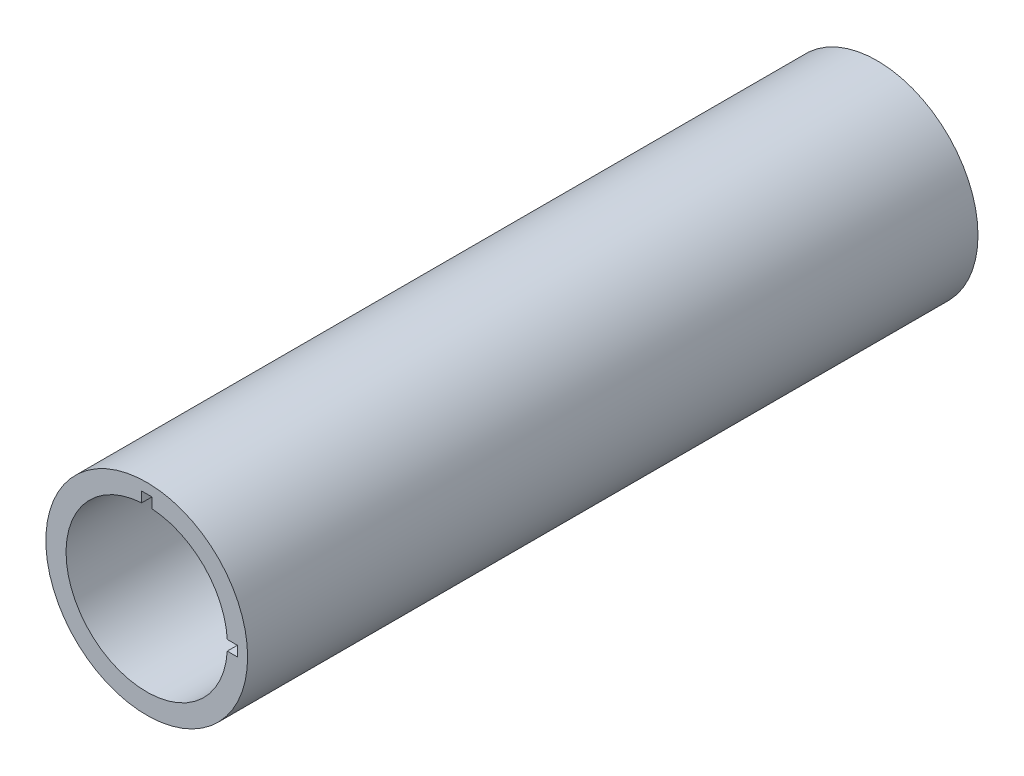
SolidWorks part; units mm, degrees
ref_plane "Front Plane" through (0, 0, 0) normal (0, 0, 1) x (1, 0, 0)
ref_plane "Top Plane" through (0, 0, 0) normal (0, 1, 0) x (1, 0, 0)
ref_plane "Right Plane" through (0, 0, 0) normal (1, 0, 0) x (0, 0, -1)
sketch "Sketch1" plane through (0, 0, 0) normal (0, 0, 1) x (1, 0, 0)
  circle A0 centre (0, 0) radius 25
  circle A1 centre (0, 0) radius 20
extrude "Boss-Extrude1" add sketch "Sketch1" along normal blind 181
ref_plane "Plane1" through (0, 22.5, 0) normal (0, 1, 0) x (-1, 0, 0)
sketch "Sketch5" plane through (0, 22.5, 0) normal (0, 1, 0) x (-1, 0, 0)
  line L1 (-1.25, 151.2302) -> (1.25, 151.2302)
  line L2 (-1.25, 151.2302) -> (-1.25, 181.2302)
  line L3 (-1.25, 181.2302) -> (1.25, 181.2302)
  line L4 (1.25, 151.2302) -> (1.25, 181.2302)
  line L5 (-1.25, 151.2302) -> (1.25, 181.2302) construction
  line L6 (-1.25, 181.2302) -> (1.25, 151.2302) construction
  point P0 (0, 166.2302)
  point P5 (0, 0)
extrude "Cut-Extrude2" cut sketch "Sketch5" against normal blind 6
pattern_circular "CirPattern8" count 2 every 90 about axis through (0, 0, 0) along (0, 0, 1) of "Cut-Extrude2"
